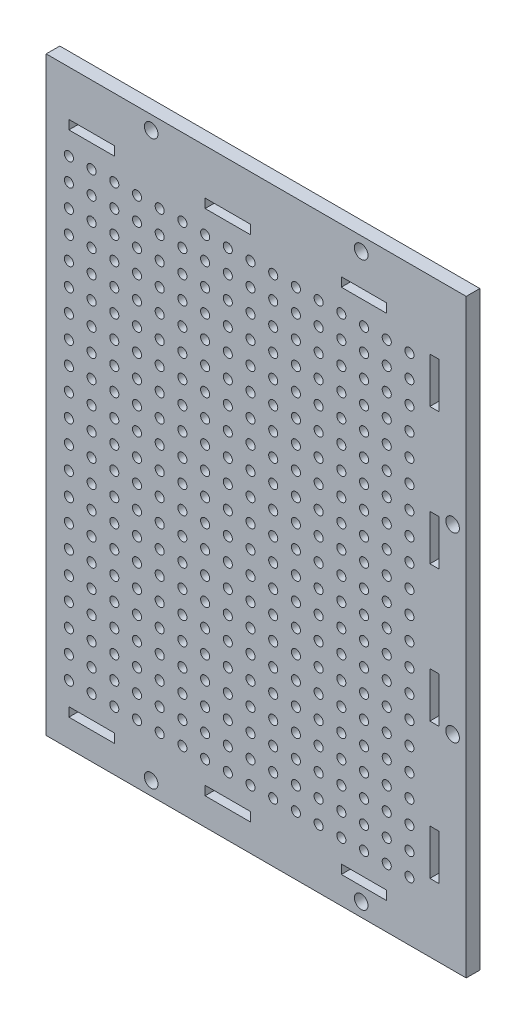
SolidWorks part; units mm, degrees
ref_plane "Plan de face" through (0, 0, 0) normal (0, 0, 1) x (1, 0, 0)
ref_plane "Plan de dessus" through (0, 0, 0) normal (0, 1, 0) x (1, 0, 0)
ref_plane "Plan de droite" through (0, 0, 0) normal (1, 0, 0) x (0, 0, -1)
sketch "Esquisse1" plane through (0, 0, 0) normal (0, 0, 1) x (1, 0, 0)
  line L1 (-77.577, 49.8492) -> (14.923, 49.8492)
  line L2 (-77.577, 49.8492) -> (-77.577, -80.1508)
  line L3 (-77.577, -80.1508) -> (14.923, -80.1508)
  line L4 (14.923, 49.8492) -> (14.923, -80.1508)
  dimension "D1" = 92.5
  dimension "D2" = 130
extrude "Boss.-Extru.1" add sketch "Esquisse1" along normal blind 3
sketch "Esquisse2" plane through (0, 0, 3) normal (0, 0, 1) x (1, 0, 0)
  line L1 (-72.577, 39.8492) -> (-62.577, 39.8492)
  line L2 (-72.577, 39.8492) -> (-72.577, 37.8492)
  line L3 (-72.577, 37.8492) -> (-62.577, 37.8492)
  line L4 (-62.577, 39.8492) -> (-62.577, 37.8492)
  line L5 (-77.577, 49.8492) -> (-77.577, -80.1508) construction
  line L6 (14.923, 49.8492) -> (-77.577, 49.8492) construction
  line L7 (20.6407, 39.8492) -> (-122.3081, 39.8492) construction
  line L8 (8.923, 57.8654) -> (8.923, -98.0996) construction
  line L9 (-42.577, 39.8492) -> (-32.577, 39.8492)
  line L10 (-42.577, 39.8492) -> (-42.577, 37.8492)
  line L11 (-42.577, 37.8492) -> (-32.577, 37.8492)
  line L12 (-32.577, 39.8492) -> (-32.577, 37.8492)
  line L13 (-2.577, 39.8492) -> (-12.577, 39.8492)
  line L14 (-2.577, 39.8492) -> (-2.577, 37.8492)
  line L15 (-2.577, 37.8492) -> (-12.577, 37.8492)
  line L16 (-12.577, 39.8492) -> (-12.577, 37.8492)
  line L17 (14.923, -80.1508) -> (14.923, 49.8492) construction
  line L18 (-94.0135, -74.1508) -> (51.0979, -74.1508) construction
  line L19 (8.923, 34.8492) -> (6.923, 34.8492)
  line L20 (8.923, 34.8492) -> (8.923, 24.8492)
  line L21 (8.923, 24.8492) -> (6.923, 24.8492)
  line L22 (6.923, 34.8492) -> (6.923, 24.8492)
  line L23 (8.923, 4.8492) -> (6.923, 4.8492)
  line L24 (8.923, 4.8492) -> (8.923, -5.1508)
  line L25 (8.923, -5.1508) -> (6.923, -5.1508)
  line L26 (6.923, 4.8492) -> (6.923, -5.1508)
  line L27 (8.923, -25.1508) -> (6.923, -25.1508)
  line L28 (8.923, -25.1508) -> (8.923, -35.1508)
  line L29 (8.923, -35.1508) -> (6.923, -35.1508)
  line L30 (6.923, -25.1508) -> (6.923, -35.1508)
  line L31 (8.923, -55.1508) -> (6.923, -55.1508)
  line L32 (8.923, -55.1508) -> (8.923, -65.1508)
  line L33 (8.923, -65.1508) -> (6.923, -65.1508)
  line L34 (6.923, -55.1508) -> (6.923, -65.1508)
  line L35 (-77.577, -80.1508) -> (14.923, -80.1508) construction
  line L36 (-72.577, 60.3986) -> (-72.577, -95.8049) construction
  line L37 (-72.577, -74.1508) -> (-62.577, -74.1508)
  line L38 (-72.577, -74.1508) -> (-72.577, -72.1508)
  line L39 (-72.577, -72.1508) -> (-62.577, -72.1508)
  line L40 (-62.577, -74.1508) -> (-62.577, -72.1508)
  line L41 (-42.577, -74.1508) -> (-32.577, -74.1508)
  line L42 (-42.577, -74.1508) -> (-42.577, -72.1508)
  line L43 (-42.577, -72.1508) -> (-32.577, -72.1508)
  line L44 (-32.577, -74.1508) -> (-32.577, -72.1508)
  line L45 (-12.577, -74.1508) -> (-2.577, -74.1508)
  line L46 (-12.577, -74.1508) -> (-12.577, -72.1508)
  line L47 (-12.577, -72.1508) -> (-2.577, -72.1508)
  line L48 (-2.577, -74.1508) -> (-2.577, -72.1508)
  line L49 (-85.9817, 7.8492) -> (29.7142, 7.8492) construction
  line L57 (-85.9817, -2.1508) -> (29.7142, -2.1508) construction
  line L58 (-85.9817, -12.1508) -> (29.7142, -12.1508) construction
  line L59 (-85.9817, -22.1508) -> (29.7142, -22.1508) construction
  line L60 (-85.9817, -32.1508) -> (29.7142, -32.1508) construction
  line L61 (-85.9817, -42.1508) -> (29.7142, -42.1508) construction
  line L62 (-85.9817, -52.1508) -> (29.7142, -52.1508) construction
  line L63 (-85.9817, -62.1508) -> (29.7142, -62.1508) construction
  circle A0 centre (-72.577, 22.8492) radius 1
  circle A1 centre (-72.577, 17.8492) radius 1
  circle A2 centre (-72.577, 12.8492) radius 1
  circle A3 centre (-72.577, 32.8492) radius 1
  circle A4 centre (-72.577, 27.8492) radius 1
  circle A5 centre (-72.577, 22.8492) radius 1
  circle A6 centre (-72.577, 22.8492) radius 1
  circle A7 centre (-67.577, 22.8492) radius 1
  circle A8 centre (-72.577, -47.1508) radius 1
  circle A9 centre (-67.577, 17.8492) radius 1
  circle A10 centre (-67.577, 12.8492) radius 1
  circle A11 centre (-72.577, 12.8492) radius 1
  circle A12 centre (-72.577, 7.8492) radius 1
  circle A13 centre (-72.577, 2.8492) radius 1
  circle A14 centre (-72.577, 2.8492) radius 1
  circle A15 centre (-72.577, -2.1508) radius 1
  circle A16 centre (-72.577, -7.1508) radius 1
  circle A17 centre (-72.577, -7.1508) radius 1
  circle A18 centre (-72.577, -12.1508) radius 1
  circle A19 centre (-72.577, -17.1508) radius 1
  circle A20 centre (-72.577, -17.1508) radius 1
  circle A21 centre (-72.577, -22.1508) radius 1
  circle A22 centre (-72.577, -27.1508) radius 1
  circle A23 centre (-72.577, -27.1508) radius 1
  circle A24 centre (-72.577, -32.1508) radius 1
  circle A25 centre (-72.577, -37.1508) radius 1
  circle A26 centre (-72.577, -37.1508) radius 1
  circle A27 centre (-72.577, -42.1508) radius 1
  circle A28 centre (-67.577, 32.8492) radius 1
  circle A29 centre (-67.577, 27.8492) radius 1
  circle A30 centre (-72.577, -52.1508) radius 1
  circle A31 centre (-72.577, -57.1508) radius 1
  circle A32 centre (-72.577, -47.1508) radius 1 [skipped]
  circle A33 centre (-72.577, -47.1508) radius 1 [skipped]
  circle A34 centre (-67.577, 22.8492) radius 1
  circle A35 centre (-67.577, 22.8492) radius 1
  circle A36 centre (-67.577, -47.1508) radius 1
  circle A37 centre (-67.577, 12.8492) radius 1
  circle A38 centre (-67.577, 7.8492) radius 1
  circle A39 centre (-67.577, 2.8492) radius 1
  circle A40 centre (-67.577, 2.8492) radius 1
  circle A41 centre (-67.577, -2.1508) radius 1
  circle A42 centre (-67.577, -7.1508) radius 1
  circle A43 centre (-67.577, -7.1508) radius 1
  circle A44 centre (-67.577, -12.1508) radius 1
  circle A45 centre (-67.577, -17.1508) radius 1
  circle A46 centre (-67.577, -17.1508) radius 1
  circle A47 centre (-67.577, -22.1508) radius 1
  circle A48 centre (-67.577, -27.1508) radius 1
  circle A49 centre (-67.577, -27.1508) radius 1
  circle A50 centre (-67.577, -32.1508) radius 1
  circle A51 centre (-67.577, -37.1508) radius 1
  circle A52 centre (-67.577, -37.1508) radius 1
  circle A53 centre (-67.577, -42.1508) radius 1
  circle A54 centre (-67.577, -52.1508) radius 1
  circle A55 centre (-67.577, -57.1508) radius 1
  circle A56 centre (-62.577, 22.8492) radius 1
  circle A57 centre (-62.577, 17.8492) radius 1
  circle A58 centre (-62.577, 12.8492) radius 1
  circle A59 centre (-62.577, 32.8492) radius 1
  circle A60 centre (-62.577, 27.8492) radius 1
  circle A61 centre (-62.577, 22.8492) radius 1
  circle A62 centre (-62.577, 22.8492) radius 1
  circle A63 centre (-62.577, -47.1508) radius 1
  circle A64 centre (-62.577, 12.8492) radius 1
  circle A65 centre (-62.577, 7.8492) radius 1
  circle A66 centre (-62.577, 2.8492) radius 1
  circle A67 centre (-62.577, 2.8492) radius 1
  circle A68 centre (-62.577, -2.1508) radius 1
  circle A69 centre (-62.577, -7.1508) radius 1
  circle A70 centre (-62.577, -7.1508) radius 1
  circle A71 centre (-62.577, -12.1508) radius 1
  circle A72 centre (-62.577, -17.1508) radius 1
  circle A73 centre (-62.577, -17.1508) radius 1
  circle A74 centre (-62.577, -22.1508) radius 1
  circle A75 centre (-62.577, -27.1508) radius 1
  circle A76 centre (-62.577, -27.1508) radius 1
  circle A77 centre (-62.577, -32.1508) radius 1
  circle A78 centre (-62.577, -37.1508) radius 1
  circle A79 centre (-62.577, -37.1508) radius 1
  circle A80 centre (-62.577, -42.1508) radius 1
  circle A81 centre (-62.577, -52.1508) radius 1
  circle A82 centre (-62.577, -57.1508) radius 1
  circle A83 centre (-57.577, 22.8492) radius 1
  circle A84 centre (-57.577, 17.8492) radius 1
  circle A85 centre (-57.577, 12.8492) radius 1
  circle A86 centre (-57.577, 32.8492) radius 1
  circle A87 centre (-57.577, 27.8492) radius 1
  circle A88 centre (-57.577, 22.8492) radius 1
  circle A89 centre (-57.577, 22.8492) radius 1
  circle A90 centre (-57.577, -47.1508) radius 1
  circle A91 centre (-57.577, 12.8492) radius 1
  circle A92 centre (-57.577, 7.8492) radius 1
  circle A93 centre (-57.577, 2.8492) radius 1
  circle A94 centre (-57.577, 2.8492) radius 1
  circle A95 centre (-57.577, -2.1508) radius 1
  circle A96 centre (-57.577, -7.1508) radius 1
  circle A97 centre (-57.577, -7.1508) radius 1
  circle A98 centre (-57.577, -12.1508) radius 1
  circle A99 centre (-57.577, -17.1508) radius 1
  circle A100 centre (-57.577, -17.1508) radius 1
  circle A101 centre (-57.577, -22.1508) radius 1
  circle A102 centre (-57.577, -27.1508) radius 1
  circle A103 centre (-57.577, -27.1508) radius 1
  circle A104 centre (-57.577, -32.1508) radius 1
  circle A105 centre (-57.577, -37.1508) radius 1
  circle A106 centre (-57.577, -37.1508) radius 1
  circle A107 centre (-57.577, -42.1508) radius 1
  circle A108 centre (-57.577, -52.1508) radius 1
  circle A109 centre (-57.577, -57.1508) radius 1
  circle A110 centre (-52.577, 22.8492) radius 1
  circle A111 centre (-52.577, 17.8492) radius 1
  circle A112 centre (-52.577, 12.8492) radius 1
  circle A113 centre (-52.577, 32.8492) radius 1
  circle A114 centre (-52.577, 27.8492) radius 1
  circle A115 centre (-52.577, 22.8492) radius 1
  circle A116 centre (-52.577, 22.8492) radius 1
  circle A117 centre (-52.577, -47.1508) radius 1
  circle A118 centre (-52.577, 12.8492) radius 1
  circle A119 centre (-52.577, 7.8492) radius 1
  circle A120 centre (-52.577, 2.8492) radius 1
  circle A121 centre (-52.577, 2.8492) radius 1
  circle A122 centre (-52.577, -2.1508) radius 1
  circle A123 centre (-52.577, -7.1508) radius 1
  circle A124 centre (-52.577, -7.1508) radius 1
  circle A125 centre (-52.577, -12.1508) radius 1
  circle A126 centre (-52.577, -17.1508) radius 1
  circle A127 centre (-52.577, -17.1508) radius 1
  circle A128 centre (-52.577, -22.1508) radius 1
  circle A129 centre (-52.577, -27.1508) radius 1
  circle A130 centre (-52.577, -27.1508) radius 1
  circle A131 centre (-52.577, -32.1508) radius 1
  circle A132 centre (-52.577, -37.1508) radius 1
  circle A133 centre (-52.577, -37.1508) radius 1
  circle A134 centre (-52.577, -42.1508) radius 1
  circle A135 centre (-52.577, -52.1508) radius 1
  circle A136 centre (-52.577, -57.1508) radius 1
  circle A137 centre (-47.577, 22.8492) radius 1
  circle A138 centre (-47.577, 17.8492) radius 1
  circle A139 centre (-47.577, 12.8492) radius 1
  circle A140 centre (-47.577, 32.8492) radius 1
  circle A141 centre (-47.577, 27.8492) radius 1
  circle A142 centre (-47.577, 22.8492) radius 1
  circle A143 centre (-47.577, 22.8492) radius 1
  circle A144 centre (-47.577, -47.1508) radius 1
  circle A145 centre (-47.577, 12.8492) radius 1
  circle A146 centre (-47.577, 7.8492) radius 1
  circle A147 centre (-47.577, 2.8492) radius 1
  circle A148 centre (-47.577, 2.8492) radius 1
  circle A149 centre (-47.577, -2.1508) radius 1
  circle A150 centre (-47.577, -7.1508) radius 1
  circle A151 centre (-47.577, -7.1508) radius 1
  circle A152 centre (-47.577, -12.1508) radius 1
  circle A153 centre (-47.577, -17.1508) radius 1
  circle A154 centre (-47.577, -17.1508) radius 1
  circle A155 centre (-47.577, -22.1508) radius 1
  circle A156 centre (-47.577, -27.1508) radius 1
  circle A157 centre (-47.577, -27.1508) radius 1
  circle A158 centre (-47.577, -32.1508) radius 1
  circle A159 centre (-47.577, -37.1508) radius 1
  circle A160 centre (-47.577, -37.1508) radius 1
  circle A161 centre (-47.577, -42.1508) radius 1
  circle A162 centre (-47.577, -52.1508) radius 1
  circle A163 centre (-47.577, -57.1508) radius 1
  circle A164 centre (-42.577, 22.8492) radius 1
  circle A165 centre (-42.577, 17.8492) radius 1
  circle A166 centre (-42.577, 12.8492) radius 1
  circle A167 centre (-42.577, 32.8492) radius 1
  circle A168 centre (-42.577, 27.8492) radius 1
  circle A169 centre (-42.577, 22.8492) radius 1
  circle A170 centre (-42.577, 22.8492) radius 1
  circle A171 centre (-42.577, -47.1508) radius 1
  circle A172 centre (-42.577, 12.8492) radius 1
  circle A173 centre (-42.577, 7.8492) radius 1
  circle A174 centre (-42.577, 2.8492) radius 1
  circle A175 centre (-42.577, 2.8492) radius 1
  circle A176 centre (-42.577, -2.1508) radius 1
  circle A177 centre (-42.577, -7.1508) radius 1
  circle A178 centre (-42.577, -7.1508) radius 1
  circle A179 centre (-42.577, -12.1508) radius 1
  circle A180 centre (-42.577, -17.1508) radius 1
  circle A181 centre (-42.577, -17.1508) radius 1
  circle A182 centre (-42.577, -22.1508) radius 1
  circle A183 centre (-42.577, -27.1508) radius 1
  circle A184 centre (-42.577, -27.1508) radius 1
  circle A185 centre (-42.577, -32.1508) radius 1
  circle A186 centre (-42.577, -37.1508) radius 1
  circle A187 centre (-42.577, -37.1508) radius 1
  circle A188 centre (-42.577, -42.1508) radius 1
  circle A189 centre (-42.577, -52.1508) radius 1
  circle A190 centre (-42.577, -57.1508) radius 1
  circle A191 centre (-37.577, 22.8492) radius 1
  circle A192 centre (-37.577, 17.8492) radius 1
  circle A193 centre (-37.577, 12.8492) radius 1
  circle A194 centre (-37.577, 32.8492) radius 1
  circle A195 centre (-37.577, 27.8492) radius 1
  circle A196 centre (-37.577, 22.8492) radius 1
  circle A197 centre (-37.577, 22.8492) radius 1
  circle A198 centre (-37.577, -47.1508) radius 1
  circle A199 centre (-37.577, 12.8492) radius 1
  circle A200 centre (-37.577, 7.8492) radius 1
  circle A201 centre (-37.577, 2.8492) radius 1
  circle A202 centre (-37.577, 2.8492) radius 1
  circle A203 centre (-37.577, -2.1508) radius 1
  circle A204 centre (-37.577, -7.1508) radius 1
  circle A205 centre (-37.577, -7.1508) radius 1
  circle A206 centre (-37.577, -12.1508) radius 1
  circle A207 centre (-37.577, -17.1508) radius 1
  circle A208 centre (-37.577, -17.1508) radius 1
  circle A209 centre (-37.577, -22.1508) radius 1
  circle A210 centre (-37.577, -27.1508) radius 1
  circle A211 centre (-37.577, -27.1508) radius 1
  circle A212 centre (-37.577, -32.1508) radius 1
  circle A213 centre (-37.577, -37.1508) radius 1
  circle A214 centre (-37.577, -37.1508) radius 1
  circle A215 centre (-37.577, -42.1508) radius 1
  circle A216 centre (-37.577, -52.1508) radius 1
  circle A217 centre (-37.577, -57.1508) radius 1
  circle A218 centre (-32.577, 22.8492) radius 1
  circle A219 centre (-32.577, 17.8492) radius 1
  circle A220 centre (-32.577, 12.8492) radius 1
  circle A221 centre (-32.577, 32.8492) radius 1
  circle A222 centre (-32.577, 27.8492) radius 1
  circle A223 centre (-32.577, 22.8492) radius 1
  circle A224 centre (-32.577, 22.8492) radius 1
  circle A225 centre (-32.577, -47.1508) radius 1
  circle A226 centre (-32.577, 12.8492) radius 1
  circle A227 centre (-32.577, 7.8492) radius 1
  circle A228 centre (-32.577, 2.8492) radius 1
  circle A229 centre (-32.577, 2.8492) radius 1
  circle A230 centre (-32.577, -2.1508) radius 1
  circle A231 centre (-32.577, -7.1508) radius 1
  circle A232 centre (-32.577, -7.1508) radius 1
  circle A233 centre (-32.577, -12.1508) radius 1
  circle A234 centre (-32.577, -17.1508) radius 1
  circle A235 centre (-32.577, -17.1508) radius 1
  circle A236 centre (-32.577, -22.1508) radius 1
  circle A237 centre (-32.577, -27.1508) radius 1
  circle A238 centre (-32.577, -27.1508) radius 1
  circle A239 centre (-32.577, -32.1508) radius 1
  circle A240 centre (-32.577, -37.1508) radius 1
  circle A241 centre (-32.577, -37.1508) radius 1
  circle A242 centre (-32.577, -42.1508) radius 1
  circle A243 centre (-32.577, -52.1508) radius 1
  circle A244 centre (-32.577, -57.1508) radius 1
  circle A245 centre (-27.577, 22.8492) radius 1
  circle A246 centre (-27.577, 17.8492) radius 1
  circle A247 centre (-27.577, 12.8492) radius 1
  circle A248 centre (-27.577, 32.8492) radius 1
  circle A249 centre (-27.577, 27.8492) radius 1
  circle A250 centre (-27.577, 22.8492) radius 1
  circle A251 centre (-27.577, 22.8492) radius 1
  circle A252 centre (-27.577, -47.1508) radius 1
  circle A253 centre (-27.577, 12.8492) radius 1
  circle A254 centre (-27.577, 7.8492) radius 1
  circle A255 centre (-27.577, 2.8492) radius 1
  circle A256 centre (-27.577, 2.8492) radius 1
  circle A257 centre (-27.577, -2.1508) radius 1
  circle A258 centre (-27.577, -7.1508) radius 1
  circle A259 centre (-27.577, -7.1508) radius 1
  circle A260 centre (-27.577, -12.1508) radius 1
  circle A261 centre (-27.577, -17.1508) radius 1
  circle A262 centre (-27.577, -17.1508) radius 1
  circle A263 centre (-27.577, -22.1508) radius 1
  circle A264 centre (-27.577, -27.1508) radius 1
  circle A265 centre (-27.577, -27.1508) radius 1
  circle A266 centre (-27.577, -32.1508) radius 1
  circle A267 centre (-27.577, -37.1508) radius 1
  circle A268 centre (-27.577, -37.1508) radius 1
  circle A269 centre (-27.577, -42.1508) radius 1
  circle A270 centre (-27.577, -52.1508) radius 1
  circle A271 centre (-27.577, -57.1508) radius 1
  circle A272 centre (-22.577, 22.8492) radius 1
  circle A273 centre (-22.577, 17.8492) radius 1
  circle A274 centre (-22.577, 12.8492) radius 1
  circle A275 centre (-22.577, 32.8492) radius 1
  circle A276 centre (-22.577, 27.8492) radius 1
  circle A277 centre (-22.577, 22.8492) radius 1
  circle A278 centre (-22.577, 22.8492) radius 1
  circle A279 centre (-22.577, -47.1508) radius 1
  circle A280 centre (-22.577, 12.8492) radius 1
  circle A281 centre (-22.577, 7.8492) radius 1
  circle A282 centre (-22.577, 2.8492) radius 1
  circle A283 centre (-22.577, 2.8492) radius 1
  circle A284 centre (-22.577, -2.1508) radius 1
  circle A285 centre (-22.577, -7.1508) radius 1
  circle A286 centre (-22.577, -7.1508) radius 1
  circle A287 centre (-22.577, -12.1508) radius 1
  circle A288 centre (-22.577, -17.1508) radius 1
  circle A289 centre (-22.577, -17.1508) radius 1
  circle A290 centre (-22.577, -22.1508) radius 1
  circle A291 centre (-22.577, -27.1508) radius 1
  circle A292 centre (-22.577, -27.1508) radius 1
  circle A293 centre (-22.577, -32.1508) radius 1
  circle A294 centre (-22.577, -37.1508) radius 1
  circle A295 centre (-22.577, -37.1508) radius 1
  circle A296 centre (-22.577, -42.1508) radius 1
  circle A297 centre (-22.577, -52.1508) radius 1
  circle A298 centre (-22.577, -57.1508) radius 1
  circle A299 centre (-17.577, 22.8492) radius 1
  circle A300 centre (-17.577, 17.8492) radius 1
  circle A301 centre (-17.577, 12.8492) radius 1
  circle A302 centre (-17.577, 32.8492) radius 1
  circle A303 centre (-17.577, 27.8492) radius 1
  circle A304 centre (-17.577, 22.8492) radius 1
  circle A305 centre (-17.577, 22.8492) radius 1
  circle A306 centre (-17.577, -47.1508) radius 1
  circle A307 centre (-17.577, 12.8492) radius 1
  circle A308 centre (-17.577, 7.8492) radius 1
  circle A309 centre (-17.577, 2.8492) radius 1
  circle A310 centre (-17.577, 2.8492) radius 1
  circle A311 centre (-17.577, -2.1508) radius 1
  circle A312 centre (-17.577, -7.1508) radius 1
  circle A313 centre (-17.577, -7.1508) radius 1
  circle A314 centre (-17.577, -12.1508) radius 1
  circle A315 centre (-17.577, -17.1508) radius 1
  circle A316 centre (-17.577, -17.1508) radius 1
  circle A317 centre (-17.577, -22.1508) radius 1
  circle A318 centre (-17.577, -27.1508) radius 1
  circle A319 centre (-17.577, -27.1508) radius 1
  circle A320 centre (-17.577, -32.1508) radius 1
  circle A321 centre (-17.577, -37.1508) radius 1
  circle A322 centre (-17.577, -37.1508) radius 1
  circle A323 centre (-17.577, -42.1508) radius 1
  circle A324 centre (-17.577, -52.1508) radius 1
  circle A325 centre (-17.577, -57.1508) radius 1
  circle A326 centre (-12.577, 22.8492) radius 1
  circle A327 centre (-12.577, 17.8492) radius 1
  circle A328 centre (-12.577, 12.8492) radius 1
  circle A329 centre (-12.577, 32.8492) radius 1
  circle A330 centre (-12.577, 27.8492) radius 1
  circle A331 centre (-12.577, 22.8492) radius 1
  circle A332 centre (-12.577, 22.8492) radius 1
  circle A333 centre (-12.577, -47.1508) radius 1
  circle A334 centre (-12.577, 12.8492) radius 1
  circle A335 centre (-12.577, 7.8492) radius 1
  circle A336 centre (-12.577, 2.8492) radius 1
  circle A337 centre (-12.577, 2.8492) radius 1
  circle A338 centre (-12.577, -2.1508) radius 1
  circle A339 centre (-12.577, -7.1508) radius 1
  circle A340 centre (-12.577, -7.1508) radius 1
  circle A341 centre (-12.577, -12.1508) radius 1
  circle A342 centre (-12.577, -17.1508) radius 1
  circle A343 centre (-12.577, -17.1508) radius 1
  circle A344 centre (-12.577, -22.1508) radius 1
  circle A345 centre (-12.577, -27.1508) radius 1
  circle A346 centre (-12.577, -27.1508) radius 1
  circle A347 centre (-12.577, -32.1508) radius 1
  circle A348 centre (-12.577, -37.1508) radius 1
  circle A349 centre (-12.577, -37.1508) radius 1
  circle A350 centre (-12.577, -42.1508) radius 1
  circle A351 centre (-12.577, -52.1508) radius 1
  circle A352 centre (-12.577, -57.1508) radius 1
  circle A353 centre (-7.577, 22.8492) radius 1
  circle A354 centre (-7.577, 17.8492) radius 1
  circle A355 centre (-7.577, 12.8492) radius 1
  circle A356 centre (-7.577, 32.8492) radius 1
  circle A357 centre (-7.577, 27.8492) radius 1
  circle A358 centre (-7.577, 22.8492) radius 1
  circle A359 centre (-7.577, 22.8492) radius 1
  circle A360 centre (-7.577, -47.1508) radius 1
  circle A361 centre (-7.577, 12.8492) radius 1
  circle A362 centre (-7.577, 7.8492) radius 1
  circle A363 centre (-7.577, 2.8492) radius 1
  circle A364 centre (-7.577, 2.8492) radius 1
  circle A365 centre (-7.577, -2.1508) radius 1
  circle A366 centre (-7.577, -7.1508) radius 1
  circle A367 centre (-7.577, -7.1508) radius 1
  circle A368 centre (-7.577, -12.1508) radius 1
  circle A369 centre (-7.577, -17.1508) radius 1
  circle A370 centre (-7.577, -17.1508) radius 1
  circle A371 centre (-7.577, -22.1508) radius 1
  circle A372 centre (-7.577, -27.1508) radius 1
  circle A373 centre (-7.577, -27.1508) radius 1
  circle A374 centre (-7.577, -32.1508) radius 1
  circle A375 centre (-7.577, -37.1508) radius 1
  circle A376 centre (-7.577, -37.1508) radius 1
  circle A377 centre (-7.577, -42.1508) radius 1
  circle A378 centre (-7.577, -52.1508) radius 1
  circle A379 centre (-7.577, -57.1508) radius 1
  circle A380 centre (-2.577, 22.8492) radius 1
  circle A381 centre (-2.577, 17.8492) radius 1
  circle A382 centre (-2.577, 12.8492) radius 1
  circle A383 centre (-2.577, 32.8492) radius 1
  circle A384 centre (-2.577, 27.8492) radius 1
  circle A385 centre (-2.577, 22.8492) radius 1
  circle A386 centre (-2.577, 22.8492) radius 1
  circle A387 centre (-2.577, -47.1508) radius 1
  circle A388 centre (-2.577, 12.8492) radius 1
  circle A389 centre (-2.577, 7.8492) radius 1
  circle A390 centre (-2.577, 2.8492) radius 1
  circle A391 centre (-2.577, 2.8492) radius 1
  circle A392 centre (-2.577, -2.1508) radius 1
  circle A393 centre (-2.577, -7.1508) radius 1
  circle A394 centre (-2.577, -7.1508) radius 1
  circle A395 centre (-2.577, -12.1508) radius 1
  circle A396 centre (-2.577, -17.1508) radius 1
  circle A397 centre (-2.577, -17.1508) radius 1
  circle A398 centre (-2.577, -22.1508) radius 1
  circle A399 centre (-2.577, -27.1508) radius 1
  circle A400 centre (-2.577, -27.1508) radius 1
  circle A401 centre (-2.577, -32.1508) radius 1
  circle A402 centre (-2.577, -37.1508) radius 1
  circle A403 centre (-2.577, -37.1508) radius 1
  circle A404 centre (-2.577, -42.1508) radius 1
  circle A405 centre (-2.577, -52.1508) radius 1
  circle A406 centre (-2.577, -57.1508) radius 1
  circle A407 centre (2.423, 22.8492) radius 1
  circle A408 centre (2.423, 17.8492) radius 1
  circle A409 centre (2.423, 12.8492) radius 1
  circle A410 centre (2.423, 32.8492) radius 1
  circle A411 centre (2.423, 27.8492) radius 1
  circle A412 centre (2.423, 22.8492) radius 1
  circle A413 centre (2.423, 22.8492) radius 1
  circle A414 centre (2.423, -47.1508) radius 1
  circle A415 centre (2.423, 12.8492) radius 1
  circle A416 centre (2.423, 7.8492) radius 1
  circle A417 centre (2.423, 2.8492) radius 1
  circle A418 centre (2.423, 2.8492) radius 1
  circle A419 centre (2.423, -2.1508) radius 1
  circle A420 centre (2.423, -7.1508) radius 1
  circle A421 centre (2.423, -7.1508) radius 1
  circle A422 centre (2.423, -12.1508) radius 1
  circle A423 centre (2.423, -17.1508) radius 1
  circle A424 centre (2.423, -17.1508) radius 1
  circle A425 centre (2.423, -22.1508) radius 1
  circle A426 centre (2.423, -27.1508) radius 1
  circle A427 centre (2.423, -27.1508) radius 1
  circle A428 centre (2.423, -32.1508) radius 1
  circle A429 centre (2.423, -37.1508) radius 1
  circle A430 centre (2.423, -37.1508) radius 1
  circle A431 centre (2.423, -42.1508) radius 1
  circle A432 centre (2.423, -52.1508) radius 1
  circle A433 centre (2.423, -57.1508) radius 1
  circle A434 centre (-72.577, -62.1508) radius 1
  circle A435 centre (-67.577, -62.1508) radius 1
  circle A436 centre (-62.577, -62.1508) radius 1
  circle A437 centre (-57.577, -62.1508) radius 1
  circle A438 centre (-52.577, -62.1508) radius 1
  circle A439 centre (-47.577, -62.1508) radius 1
  circle A440 centre (-42.577, -62.1508) radius 1
  circle A441 centre (-37.577, -62.1508) radius 1
  circle A442 centre (-32.577, -62.1508) radius 1
  circle A443 centre (-27.577, -62.1508) radius 1
  circle A444 centre (-22.577, -62.1508) radius 1
  circle A445 centre (-17.577, -62.1508) radius 1
  circle A446 centre (-12.577, -62.1508) radius 1
  circle A447 centre (-7.577, -62.1508) radius 1
  circle A448 centre (-2.577, -62.1508) radius 1
  circle A449 centre (2.423, -62.1508) radius 1
  circle A450 centre (-72.577, -67.1508) radius 1
  circle A451 centre (-67.577, -67.1508) radius 1
  circle A452 centre (-62.577, -67.1508) radius 1
  circle A453 centre (-57.577, -67.1508) radius 1
  circle A454 centre (-52.577, -67.1508) radius 1
  circle A455 centre (-47.577, -67.1508) radius 1
  circle A456 centre (-42.577, -67.1508) radius 1
  circle A457 centre (-37.577, -67.1508) radius 1
  circle A458 centre (-32.577, -67.1508) radius 1
  circle A459 centre (-27.577, -67.1508) radius 1
  circle A460 centre (-22.577, -67.1508) radius 1
  circle A461 centre (-17.577, -67.1508) radius 1
  circle A462 centre (-12.577, -67.1508) radius 1
  circle A463 centre (-7.577, -67.1508) radius 1
  circle A464 centre (-2.577, -67.1508) radius 1
  circle A465 centre (2.423, -67.1508) radius 1
  dimension "D35" = 2
  dimension "D36" = 2
  dimension "D37" = 16
  dimension "D38" = 3
  dimension "D39" = 5
  dimension "D40" = 5
  dimension "D42" = 2
  dimension "D43" = 2
  dimension "D44" = 2
  dimension "D45" = 5
  dimension "D46" = 5
  dimension "D1" = 2
  dimension "D2" = 10
  dimension "D3" = 5
  dimension "D4" = 10
  dimension "D5" = 2
  dimension "D6" = 2
  dimension "D7" = 10
  dimension "D8" = 10
  dimension "D9" = 20
  dimension "D10" = 20
  dimension "D11" = 6
  dimension "D12" = 2
  dimension "D13" = 10
  dimension "D14" = 5
  dimension "D15" = 10
  dimension "D16" = 10
  dimension "D17" = 10
  dimension "D18" = 2
  dimension "D19" = 2
  dimension "D20" = 2
  dimension "D21" = 20
  dimension "D22" = 20
  dimension "D23" = 20
  dimension "D24" = 6
  dimension "D25" = 2
  dimension "D26" = 2
  dimension "D27" = 2
  dimension "D28" = 10
  dimension "D29" = 10
  dimension "D30" = 10
  dimension "D31" = 5
  dimension "D32" = 20
  dimension "D33" = 20
  dimension "D34" = 5
  dimension "D47" = 5
  dimension "D48" = 8
extrude "Enlèv. mat.-Extru.1" cut sketch "Esquisse2" against normal blind 3
sketch "Esquisse3" plane through (0, 0, 3) normal (0, 0, 1) x (1, 0, 0)
  line L0 (-77.577, -80.1508) -> (14.923, -80.1508) construction
  line L1 (14.923, -80.1508) -> (14.923, 49.8492) construction
  line L2 (14.923, 49.8492) -> (-77.577, 49.8492) construction
  line L3 (-77.577, 49.8492) -> (-77.577, -80.1508) construction
  circle A0 centre (-54.452, -77.1508) radius 1.5
  circle A1 centre (11.923, 4.8492) radius 1.5
  circle A2 centre (11.923, -35.1508) radius 1.5
  circle A3 centre (-8.202, -77.1508) radius 1.5
  dimension "D1" = 3
  dimension "D2" = 3
  dimension "D3" = 3
  dimension "D4" = 3
  dimension "D5" = 3
  dimension "D6" = 3
  dimension "D7" = 45
  dimension "D9" = 23.125
  dimension "D10" = 3
  dimension "D11" = 3
  dimension "D12" = 23.125
  dimension "D8" = 45
extrude "Enlèv. mat.-Extru.2" cut sketch "Esquisse3" against normal blind 3
sketch "Esquisse4" plane through (0, 0, 3) normal (0, 0, 1) x (1, 0, 0)
  line L0 (14.923, 49.8492) -> (-77.577, 49.8492) construction
  line L1 (-77.577, 49.8492) -> (-77.577, -80.1508) construction
  line L2 (14.923, -80.1508) -> (14.923, 49.8492) construction
  circle A0 centre (-54.452, 46.8492) radius 1.5
  circle A1 centre (-8.202, 46.8492) radius 1.5
  dimension "D1" = 3
  dimension "D2" = 3
  dimension "D3" = 3
  dimension "D4" = 3
  dimension "D5" = 23.125
  dimension "D6" = 23.125
extrude "Enlèv. mat.-Extru.3" cut sketch "Esquisse4" against normal blind 3
